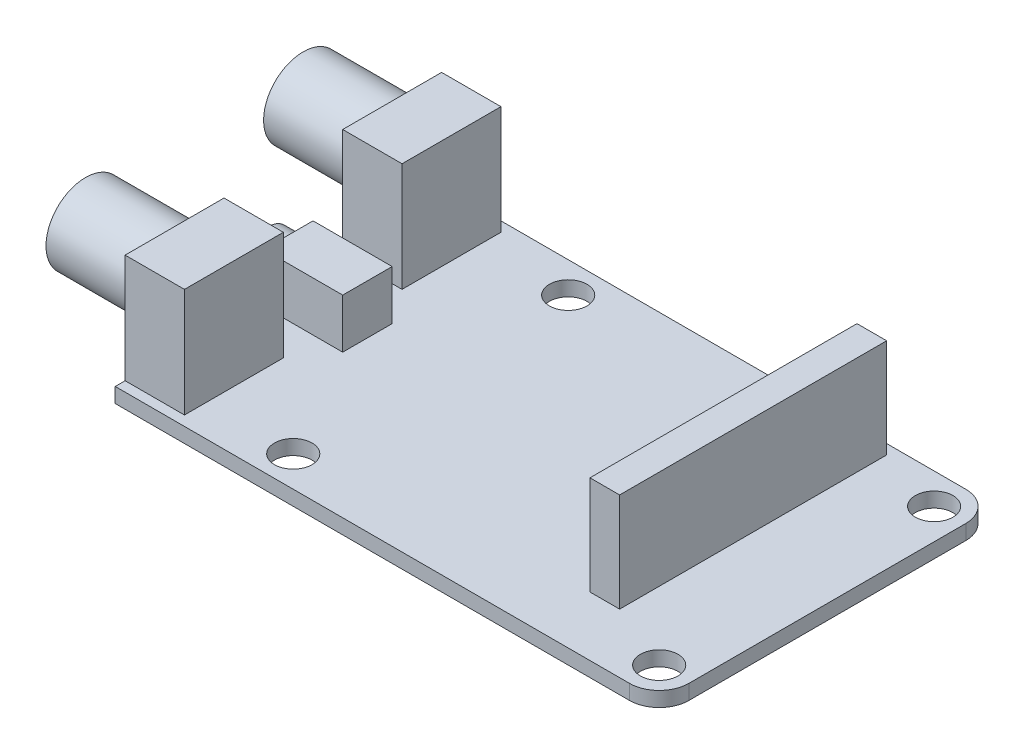
SolidWorks part; units mm, degrees
ref_plane "Front" through (0, 0, 0) normal (0, 0, 1) x (1, 0, 0)
ref_plane "Top" through (0, 0, 0) normal (0, 1, 0) x (1, 0, 0)
ref_plane "Right" through (0, 0, 0) normal (1, 0, 0) x (0, 0, -1)
sketch "Sketch1" plane through (0, 0, 0) normal (0, 1, 0) x (1, 0, 0)
  line L1 (0, 0) -> (55, 0)
  line L2 (0, 0) -> (0, -34)
  line L3 (0, -34) -> (55, -34)
  line L4 (55, 0) -> (55, -34)
  dimension "D1" = 55
  dimension "D2" = 34
extrude "Boss-Extrude1" add sketch "Sketch1" along normal blind 1.5
sketch "Sketch2" plane through (0, 1.5, 0) normal (0, 1, 0) x (1, 0, 0)
  line L0 (0, -34) -> (55, -34) construction
  line L1 (55, -34) -> (55, 0) construction
  line L2 (55, 0) -> (0, 0) construction
  circle A0 centre (51.9, -30.9) radius 1.9
  circle A1 centre (14.9, -30.9) radius 1.9
  circle A2 centre (14.9, -3.1) radius 1.9
  circle A3 centre (51.9, -3.1) radius 1.9
  point P6 (0, 0)
  dimension "D1" = 3.8
  dimension "D10" = 3.8
  dimension "D11" = 3.8
  dimension "D12" = 3.8
  dimension "D2" = 3.1
  dimension "D3" = 3.1
  dimension "D4" = 3.1
  dimension "D5" = 3.1
  dimension "D6" = 3.1
  dimension "D7" = 3.1
  dimension "D8" = 37
  dimension "D9" = 37
extrude "Cut-Extrude1" cut sketch "Sketch2" against normal through all
fillet "Fillet1" radius 3 2 edges at (55, 0.75, 0) (55, 0.75, 34)
sketch "Sketch3" plane through (0, 1.5, 0) normal (0, 1, 0) x (1, 0, 0)
  line L0 (0, -34) -> (52, -34) construction
  line L1 (0.5, -19.5) -> (8.5, -19.5)
  line L2 (0.5, -19.5) -> (0.5, -14.5)
  line L3 (0.5, -14.5) -> (8.5, -14.5)
  line L4 (8.5, -19.5) -> (8.5, -14.5)
  line L5 (0, 0) -> (0, -34) construction
  point P4 (8.5, -17)
  dimension "D1" = 17
  dimension "D2" = 0.5
  dimension "D3" = 8
  dimension "D4" = 5
extrude "Boss-Extrude2" add sketch "Sketch3" along normal blind 5
sketch "Sketch4" plane through (0.5, 0, 0) normal (-1, 0, 0) x (0, 0, 1)
  line L0 (19.5, 6.5) -> (19.5, 1.5) construction
  line L1 (14.5, 6.5) -> (19.5, 6.5) construction
  circle A0 centre (17, 4) radius 2.25
  dimension "D3" = 4.5
  dimension "D1" = 2.5
  dimension "D2" = 2.5
extrude "Boss-Extrude3" add sketch "Sketch4" along normal blind 2
sketch "Sketch5" plane through (0, 1.5, 0) normal (0, 1, 0) x (1, 0, 0)
  line L0 (52, 0) -> (0, 0) construction
  line L1 (42, -1) -> (45, -1)
  line L2 (42, -1) -> (42, -28)
  line L3 (42, -28) -> (45, -28)
  line L4 (45, -1) -> (45, -28)
  line L5 (0, -34) -> (52, -34) construction
  line L6 (55, -31) -> (55, -3) construction
  dimension "D1" = 3
  dimension "D2" = 1
  dimension "D3" = 6
  dimension "D4" = 10
extrude "Boss-Extrude4" add sketch "Sketch5" along normal blind 10
sketch "Sketch6" plane through (0, 1.5, 0) normal (0, 1, 0) x (1, 0, 0)
  line L0 (0, 0) -> (0, -34) construction
  line L1 (0, -11) -> (6, -11)
  line L2 (0, -11) -> (0, -1)
  line L3 (0, -1) -> (6, -1)
  line L4 (6, -11) -> (6, -1)
  line L5 (52, 0) -> (0, 0) construction
  line L6 (0, -23) -> (6, -23)
  line L7 (0, -23) -> (0, -33)
  line L8 (0, -33) -> (6, -33)
  line L9 (6, -23) -> (6, -33)
  line L10 (0, -34) -> (52, -34) construction
  dimension "D1" = 10
  dimension "D2" = 10
  dimension "D3" = 6
  dimension "D4" = 6
  dimension "D5" = 1
  dimension "D6" = 1
extrude "Boss-Extrude5" add sketch "Sketch6" along normal blind 11
sketch "Sketch7" plane through (0, 0, 0) normal (-1, 0, 0) x (0, 0, 1)
  line L0 (1, 12.5) -> (11, 12.5) construction
  line L1 (23, 12.5) -> (33, 12.5) construction
  line L2 (33, 12.5) -> (33, 1.5) construction
  line L3 (1, 12.5) -> (1, 1.5) construction
  circle A0 centre (28, 8.3) radius 4
  circle A1 centre (6, 8.3) radius 4
  dimension "D1" = 8
  dimension "D2" = 8
  dimension "D3" = 4.2
  dimension "D4" = 4.2
  dimension "D5" = 5
  dimension "D6" = 5
extrude "Boss-Extrude6" add sketch "Sketch7" along normal blind 9
equation "\"adc_l\"=55"
equation "\"D1@Sketch1\"=\"adc_l\""
equation "\"adc_w\"=34"
equation "\"D2@Sketch1\"=\"adc_w\""
equation "\"ho_dis\"=3.1"
equation "\"D2@Sketch2\"=\"ho_dis\""
equation "\"D3@Sketch2\"=\"ho_dis\""
equation "\"D4@Sketch2\"=\"ho_dis\""
equation "\"D5@Sketch2\"=\"ho_dis\""
equation "\"D6@Sketch2\"=\"ho_dis\""
equation "\"D7@Sketch2\"=\"ho_dis\""
equation "\"ho_dis_1\"=37"
equation "\"D8@Sketch2\"=\"ho_dis_1\""
equation "\"D9@Sketch2\"=\"ho_dis_1\""
equation "\"D1@Sketch3\"=\"adc_w\"/2"
equation "\"h_r\"=3.8"
equation "\"D1@Sketch2\"=\"h_r\""
equation "\"D10@Sketch2\"=\"h_r\""
equation "\"D11@Sketch2\"=\"h_r\""
equation "\"D12@Sketch2\"=\"h_r\""
